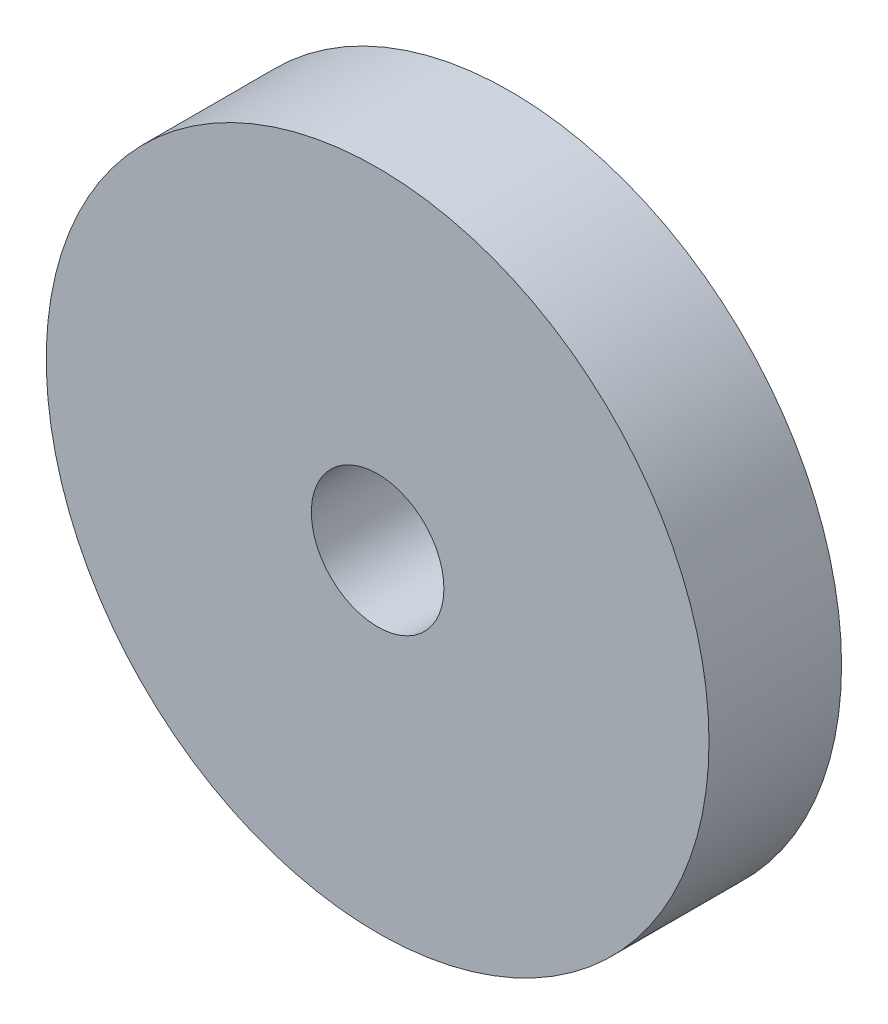
SolidWorks part; units mm, degrees
ref_plane "Front" through (0, 0, 0) normal (0, 0, 1) x (1, 0, 0)
ref_plane "Top" through (0, 0, 0) normal (0, 1, 0) x (1, 0, 0)
ref_plane "Right" through (0, 0, 0) normal (1, 0, 0) x (0, 0, -1)
sketch "Sketch1" plane through (0, 0, 0) normal (0, 0, 1) x (1, 0, 0)
  circle A0 centre (0, 0) radius 5
  circle A1 centre (0, 0) radius 1
  dimension "D1" = 2
  dimension "D2" = 10
extrude "Boss-Extrude1" add sketch "Sketch1" along normal blind 2
